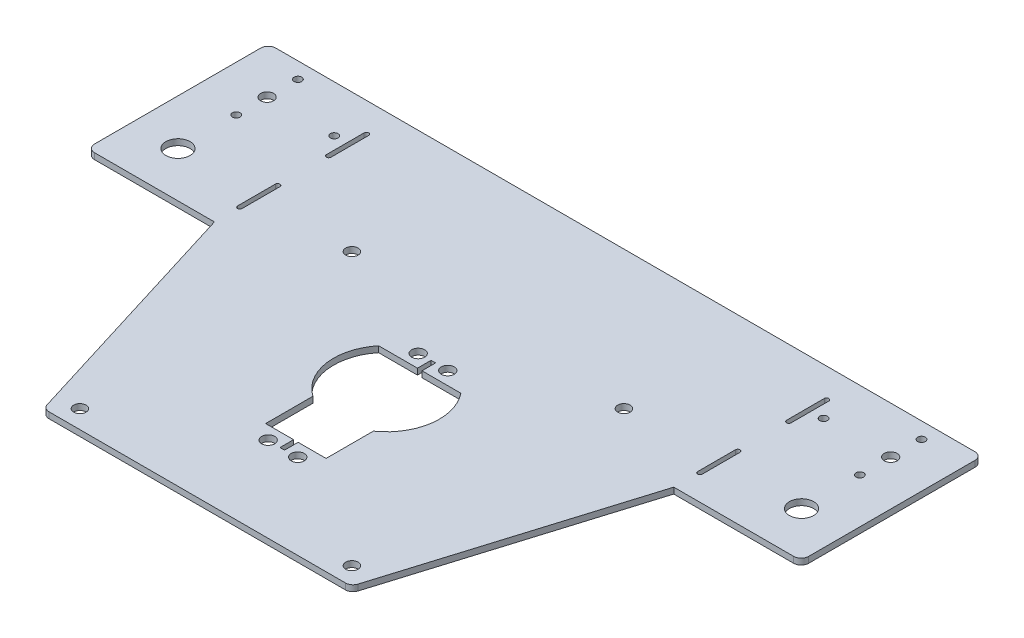
SolidWorks part; units mm, degrees
ref_plane "Front Plane" through (0, 0, 0) normal (0, 0, 1) x (1, 0, 0)
ref_plane "Top Plane" through (0, 0, 0) normal (0, 1, 0) x (1, 0, 0)
ref_plane "Right Plane" through (0, 0, 0) normal (1, 0, 0) x (0, 0, -1)
sketch "Sketch26" plane through (0, 0, 0) normal (0, 1, 0) x (1, 0, 0)
  line L0 (50.7672, 90.7668) -> (75.7672, 90.7668)
  line L1 (-76.2788, 30.7668) -> (-76.2788, 90.7668) construction
  line L3 (-49.1827, -51.0332) -> (48.9171, -51.0332)
  line L4 (-76.2788, 81.0951) -> (-76.2788, 68.5951) construction
  line L5 (-75.5288, 81.0951) -> (-75.5288, 68.5951)
  line L6 (-77.0288, 81.0951) -> (-77.0288, 68.5951)
  line L7 (-51.0328, 90.7668) -> (50.7672, 90.7668)
  line L8 (-76.2788, 39.1911) -> (-76.2788, 51.6911) construction
  line L9 (-77.0288, 39.1911) -> (-77.0288, 51.6911)
  line L10 (75.7672, 30.7668) -> (51.308, -49.2639)
  line L11 (50.7672, -61.7332) -> (50.8029, -61.7667)
  line L12 (-75.5288, 39.1911) -> (-75.5288, 51.6911)
  line L13 (-76.2788, 30.7668) -> (-51.5714, -49.2706)
  line L14 (0, 51.2) -> (0, 26.95) construction
  line L15 (-51.0328, 90.7668) -> (-76.2788, 90.7668)
  line L17 (117.9432, 33.2668) -> (117.9432, 88.2668)
  line L18 (75.7672, 90.7668) -> (115.4432, 90.7668)
  line L19 (-0.75, 22.45) -> (-0.75, 26.95)
  line L20 (75.7672, 30.7668) -> (115.4432, 30.7668)
  line L21 (-76.2788, 30.7668) -> (-115.9548, 30.7668)
  line L22 (-0.75, 26.95) -> (0.75, 26.95)
  line L23 (-76.2788, 90.7668) -> (-115.9548, 90.7668)
  line L24 (-118.4548, 33.2668) -> (-118.4548, 88.2668)
  line L25 (-51.2, -51.2) -> (51.2, -51.2)
  line L26 (0.75, 22.45) -> (0.75, 26.95)
  line L27 (0.75, -18.55) -> (0.75, -23.05)
  line L28 (-0.75, -23.05) -> (0.75, -23.05)
  line L32 (-10, -18.55) -> (-0.75, -18.55)
  line L33 (76.0133, 81.0951) -> (76.0133, 68.5951) construction
  line L34 (-10, 22.45) -> (10, -18.55) construction
  line L35 (10, 22.45) -> (-10, -18.55) construction
  line L36 (-0.75, -18.55) -> (-0.75, -23.05)
  line L37 (75.2633, 81.0951) -> (75.2633, 68.5951)
  line L38 (0.75, -18.55) -> (10, -18.55)
  line L39 (0, -23.05) -> (0, -51.2) construction
  line L41 (24.7721, 1.95) -> (-25.087, 1.95) construction
  line L42 (-10, -18.55) -> (-0.75, -18.55)
  line L44 (0.75, -18.55) -> (10, -18.55)
  line L45 (13.6107, 22.45) -> (0.75, 22.45)
  line L46 (10, 22.45) -> (13.6107, 22.45)
  line L47 (76.7633, 81.0951) -> (76.7633, 68.5951)
  line L48 (76.0133, 39.1911) -> (76.0133, 51.6911) construction
  line L49 (76.7633, 39.1911) -> (76.7633, 51.6911)
  line L50 (75.2633, 39.1911) -> (75.2633, 51.6911)
  line L51 (10, -18.55) -> (10, -2.9114)
  line L52 (-10, -18.55) -> (-10, -2.9114)
  line L53 (-0.75, 22.45) -> (-13.6107, 22.45)
  circle A0 centre (45.02, -45.02) radius 2.05
  circle A1 centre (-45.02, -45.02) radius 2.05
  circle A2 centre (-45.02, 45.02) radius 2.05
  circle A3 centre (45.02, 45.02) radius 2.05
  circle A4 centre (103.0672, 45.7668) radius 4
  arc A5 (117.9432, 33.2668) -> (115.4432, 30.7668) centre (115.4432, 33.2668) cw
  circle A6 centre (103.0672, 75.2668) radius 2.1413
  circle A7 centre (103.0672, 85.4668) radius 1.27
  circle A8 centre (103.0672, 65.0668) radius 1.27
  circle A9 centre (80.8672, 75.2668) radius 1.27
  arc A10 (117.9432, 88.2668) -> (115.4432, 90.7668) centre (115.4432, 88.2668) ccw
  arc A11 (-118.4548, 88.2668) -> (-115.9548, 90.7668) centre (-115.9548, 88.2668) cw
  arc A12 (-75.5288, 81.0951) -> (-77.0288, 81.0951) centre (-76.2788, 81.0951) ccw
  arc A13 (-77.0288, 68.5951) -> (-75.5288, 68.5951) centre (-76.2788, 68.5951) ccw
  arc A14 (-77.0288, 39.1911) -> (-75.5288, 39.1911) centre (-76.2788, 39.1911) ccw
  arc A15 (-75.5288, 51.6911) -> (-77.0288, 51.6911) centre (-76.2788, 51.6911) ccw
  arc A16 (-118.4548, 33.2668) -> (-115.9548, 30.7668) centre (-115.9548, 33.2668) ccw
  arc A17 (75.2633, 81.0951) -> (76.7633, 81.0951) centre (76.0133, 81.0951) cw
  arc A18 (-49.1827, -51.0332) -> (-51.5714, -49.2706) centre (-49.1827, -48.5332) cw
  arc A19 (51.308, -49.2639) -> (48.9171, -51.0332) centre (48.9171, -48.5332) cw
  arc A20 (76.7633, 68.5951) -> (75.2633, 68.5951) centre (76.0133, 68.5951) cw
  arc A21 (76.7633, 39.1911) -> (75.2633, 39.1911) centre (76.0133, 39.1911) cw
  arc A22 (75.2633, 51.6911) -> (76.7633, 51.6911) centre (76.0133, 51.6911) cw
  circle A23 centre (-81.1328, 75.2668) radius 1.27
  circle A24 centre (-103.3328, 65.0668) radius 1.27
  circle A25 centre (-103.3328, 85.4668) radius 1.27
  circle A26 centre (-103.3328, 75.2668) radius 2.1413
  circle A27 centre (-103.3328, 45.7668) radius 4
  circle A28 centre (-4.8452, -22.8795) radius 2.15
  circle A29 centre (4.9548, -22.8795) radius 2.15
  circle A30 centre (4.9548, 26.7795) radius 2.15
  arc A31 (13.6107, 22.45) -> (10, -2.9114) centre (0, 11.45) cw
  arc A34 (-10, -2.9114) -> (-13.6107, 22.45) centre (0, 11.45) cw
  circle A36 centre (-4.8452, 26.7795) radius 2.15
  point P13 (0, 0)
  point P16 (0, 22.45)
  point P45 (-76.2788, 74.8451)
  point P55 (-76.2788, 45.4411)
  point P63 (76.0133, 74.8451)
  point P71 (76.0133, 45.4411)
  point P89 (0, 1.95)
  point P111 (0, -18.55)
  dimension "D6" = 1.5
  dimension "D13" = 8
  dimension "D14" = 2.54
  dimension "D15" = 2.54
  dimension "D16" = 2.54
  dimension "D10" = 2.5
  dimension "D21" = 2.5
  dimension "D3" = 2.5
  dimension "D7" = 2.5
  dimension "D8" = 102.4
  dimension "D22" = 4.1
  dimension "D11" = 4.1
  dimension "D23" = 4.1
  dimension "D24" = 4.1
  dimension "D4" = 25
  dimension "D5" = 60
  dimension "D12" = 15
  dimension "D17" = 10.2
  dimension "D18" = 10.2
  dimension "D19" = 22.2
  dimension "D20" = 29.5
  dimension "D28" = 41
  dimension "D29" = 20
extrude "Boss-Extrude4" add sketch "Sketch26" along normal blind 2
